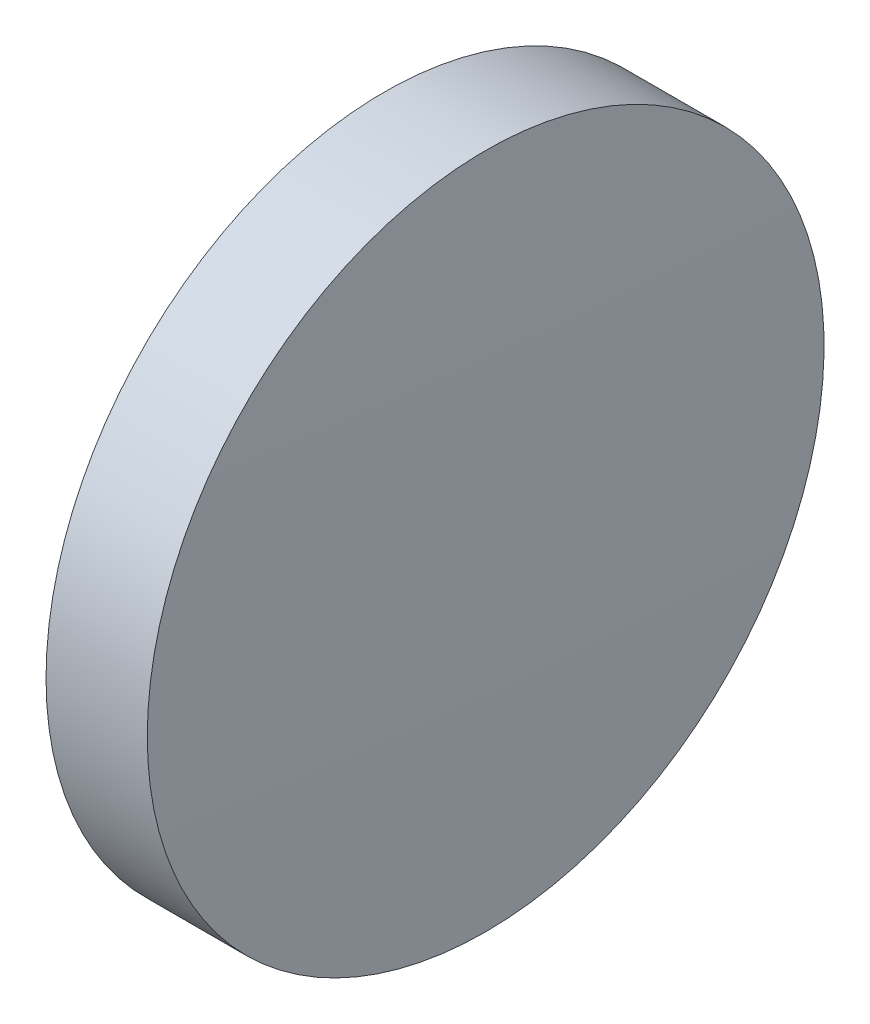
SolidWorks part; units mm, degrees
ref_plane "前视基准面" through (0, 0, 0) normal (0, 0, 1) x (1, 0, 0)
ref_plane "上视基准面" through (0, 0, 0) normal (0, 1, 0) x (1, 0, 0)
ref_plane "右视基准面" through (0, 0, 0) normal (1, 0, 0) x (0, 0, -1)
sketch "草图1" plane through (0, 0, 0) normal (0, 0, 1) x (1, 0, 0)
  line L0 (110.1654, 65.2336) -> (128.9614, 65.2336) construction
  line L1 (115.7646, 65.2336) -> (115.7646, 77.9336)
  line L2 (119.7646, 65.2336) -> (115.7646, 65.2336)
  line L5 (115.7646, 77.9336) -> (119.5646, 77.9336)
  arc A0 (119.7646, 65.2336) -> (119.5646, 77.9336) centre (-283.5604, 65.2336) ccw
revolve "旋转1" add sketch "草图1" angle 360 about L0
